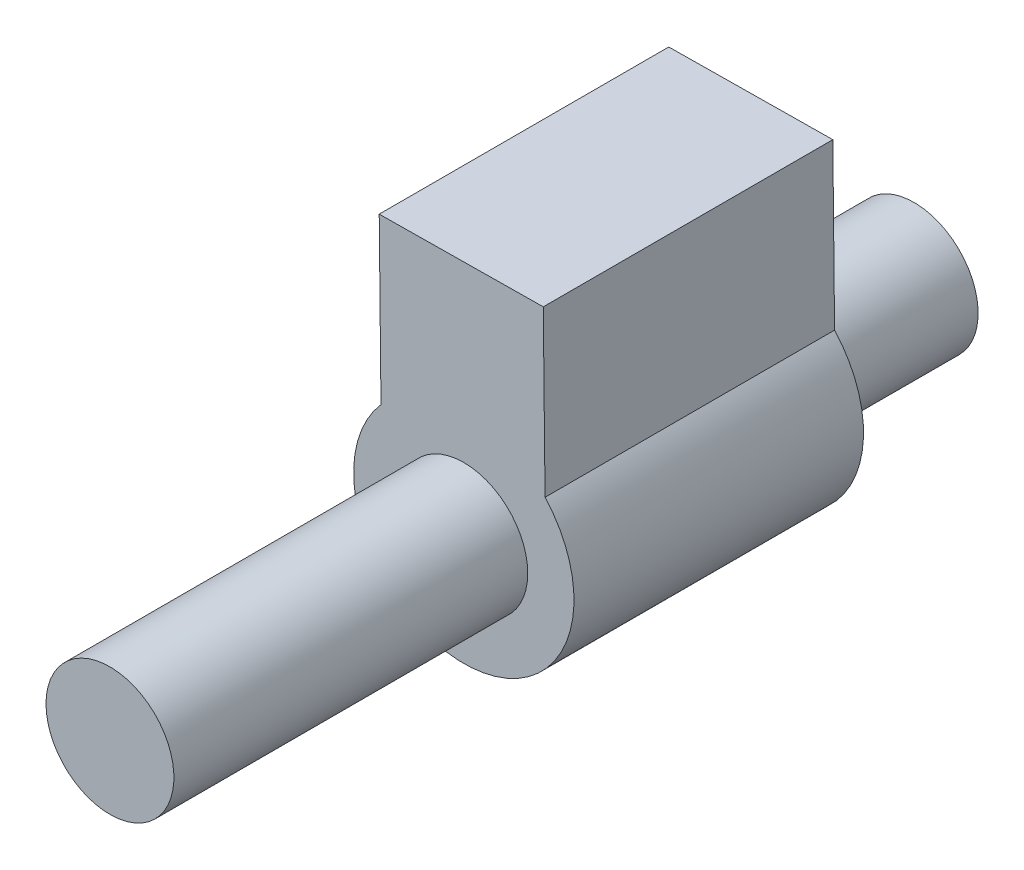
SolidWorks part; units mm, degrees
ref_plane "Front Plane" through (0, 0, 0) normal (0, 0, 1) x (1, 0, 0)
ref_plane "Top Plane" through (0, 0, 0) normal (0, 1, 0) x (1, 0, 0)
ref_plane "Right Plane" through (0, 0, 0) normal (1, 0, 0) x (0, 0, -1)
sketch "Sketch1" plane through (0, 0, 0) normal (0, 0, 1) x (1, 0, 0)
  line L0 (0.8107, 6.2559) -> (11.0107, 6.3657)
  line L1 (0.8107, 6.2559) -> (0.7008, 16.4559)
  line L2 (11.0107, 6.3657) -> (10.9008, 16.5657)
  line L3 (0.7008, 16.4559) -> (10.9008, 16.5657)
  circle A0 centre (5.9599, 1.7384) radius 6.85
  dimension "D1" = 13.7
  dimension "D2" = 6.85
  dimension "D3" = 6.85
  dimension "D4" = 10.2
  dimension "D5" = 10.2
extrude "Boss-Extrude1" add sketch "Sketch1" along normal blind 18 contours A0 L2 L3 L1 | L0 A0 | L0 A0
sketch "Sketch4" plane through (0, 0, 0) normal (0, 0, -1) x (-1, 0, 0)
  circle A0 centre (-5.9599, 1.7384) radius 3.975
  arc A1 (-11.0107, 6.3657) -> (-0.8107, 6.2559) centre (-5.9599, 1.7384) ccw construction
  dimension "D1" = 0
  dimension "D2" = 7.95
extrude "Boss-Extrude2" add sketch "Sketch4" along normal blind 10 and the other way blind 40
